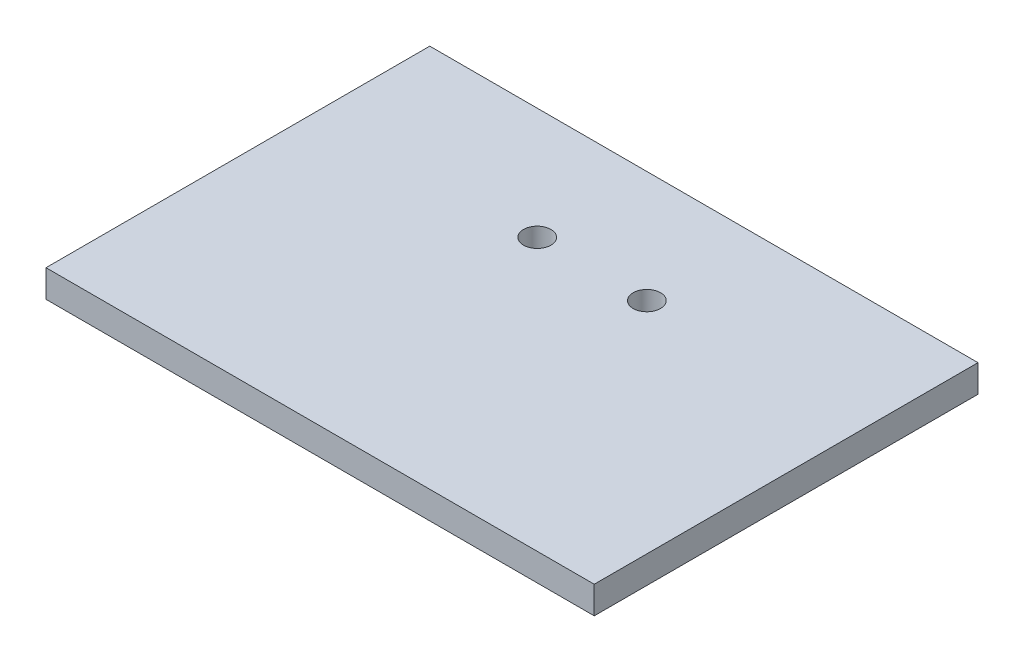
SolidWorks part; units mm, degrees
ref_plane "Front" through (0, 0, 0) normal (0, 0, 1) x (1, 0, 0)
ref_plane "Top" through (0, 0, 0) normal (0, 1, 0) x (1, 0, 0)
ref_plane "Right" through (0, 0, 0) normal (1, 0, 0) x (0, 0, -1)
sketch "Sketch1" plane through (0, 0, 0) normal (0, 0, 1) x (1, 0, 0)
  line L1 (0, 0) -> (63.5, 0)
  line L2 (0, 0) -> (0, 3.175)
  line L3 (0, 3.175) -> (63.5, 3.175)
  line L4 (63.5, 0) -> (63.5, 3.175)
  dimension "D1" = 63.5
  dimension "D2" = 3.175
extrude "Boss-Extrude1" add sketch "Sketch1" along normal blind 44.45
sketch "Sketch2" plane through (0, 3.175, 0) normal (0, 1, 0) x (1, 0, 0)
  line L0 (0, -44.45) -> (0, 0) construction
  line L1 (63.5, 0) -> (0, 0) construction
  line L2 (63.5, -44.45) -> (63.5, 0) construction
  circle A0 centre (25.4, -12.954) radius 1.5875
  circle A1 centre (38.1, -12.954) radius 1.5875
  dimension "D2" = 3.175
  dimension "D4" = 3.175
  dimension "D5" = 25.4
  dimension "D1" = 25.4
  dimension "D3" = 12.954
  dimension "D6" = 12.954
extrude "Cut-Extrude1" cut sketch "Sketch2" against normal through all
